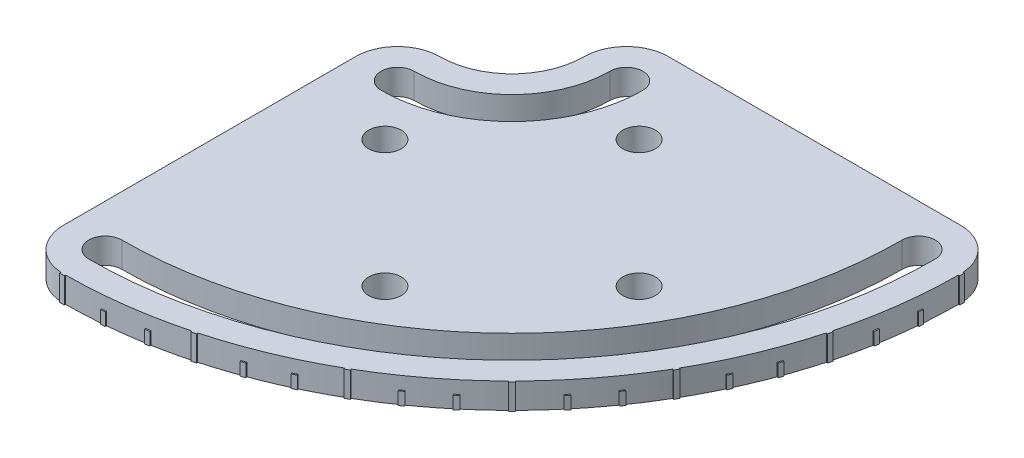
SolidWorks part; units mm, degrees
ref_plane "정면" through (0, 0, 0) normal (0, 0, 1) x (1, 0, 0)
ref_plane "윗면" through (0, 0, 0) normal (0, 1, 0) x (1, 0, 0)
ref_plane "우측면" through (0, 0, 0) normal (1, 0, 0) x (0, 0, -1)
sketch "스케치1" plane through (0, 0, 0) normal (0, 1, 0) x (1, 0, 0)
  line L1 (-8.25, -80) -> (-8.25, -22.5)
  line L7 (22.5, 8.25) -> (80, 8.25)
  arc A0 (0, -19.25) -> (0, -25.75) centre (0, -22.5) ccw
  arc A1 (25.75, 0) -> (19.25, 0) centre (22.5, 0) ccw
  arc A2 (0, -76.75) -> (0, -83.25) centre (0, -80) ccw
  arc A3 (83.25, 0) -> (76.75, 0) centre (80, 0) ccw
  arc A4 (0, -25.75) -> (25.75, 0) centre (0, 0) ccw
  arc A5 (0, -19.25) -> (19.25, 0) centre (0, 0) ccw
  arc A6 (0, -76.75) -> (76.75, 0) centre (0, 0) ccw
  arc A7 (0, -83.25) -> (83.25, 0) centre (0, 0) ccw
  circle A8 centre (58.75, -33.75) radius 3.2
  circle A9 centre (33.75, -58.75) radius 3.2
  circle A10 centre (8.75, -33.75) radius 3.2
  circle A11 centre (33.75, -8.75) radius 3.2
  arc A12 (0, -88.25) -> (88.25, 0) centre (0, 0) ccw
  arc A13 (0, -14.25) -> (14.25, 0) centre (0, 0) ccw
  arc A15 (-8.25, -80) -> (0, -88.25) centre (0, -80) ccw
  arc A16 (88.25, 0) -> (80, 8.25) centre (80, 0) ccw
  arc A17 (0, -14.25) -> (-8.25, -22.5) centre (0, -22.5) ccw
  arc A18 (22.5, 8.25) -> (14.25, 0) centre (22.5, 0) ccw
  point P0 (33.75, -33.75)
  point P26 (8.75, -33.75)
  point P27 (0, 0)
  dimension "D7" = 25
  dimension "D10" = 6.4
  dimension "D3" = 6.5
  dimension "D6" = 25
  dimension "D14" = 5
  dimension "D1" = 33.75
  dimension "D2" = 33.75
  dimension "D4" = 22.5
  dimension "D5" = 80
  dimension "D8" = 25
  dimension "D9" = 25
extrude "보스-돌출1" add sketch "스케치1" along normal blind 5
sketch "스케치2" plane through (0, 5, 0) normal (0, 1, 0) x (1, 0, 0)
  line L0 (0, 0) -> (-0.4634, -88.4988) construction
  line L1 (0, 0) -> (0.4634, -88.4988) construction
  line L2 (0, 0) -> (0, -88.5) construction
  line L3 (0.4581, -87.4988) -> (0.4634, -88.4988)
  line L4 (-0.4581, -87.4988) -> (-0.4634, -88.4988)
  arc A0 (-0.4634, -88.4988) -> (0.4634, -88.4988) centre (0, 0) ccw
  arc A1 (-0.4581, -87.4988) -> (0.4581, -87.4988) centre (0, 0) ccw
  dimension "D3" = 175
  dimension "D4" = 88.5
  dimension "D1" = 0.3
  dimension "D2" = 0.3
extrude "보스-돌출2" add sketch "스케치2" against normal up to surface (5 mm away) up to face at (12.7675, 0, 12.7675)
pattern_circular "원형 패턴1" count 7 over 90 about axis through (0, 0, 0) along (0, 1, 0) of "보스-돌출2"
sketch "스케치6" plane through (0, 0, 0) normal (0, -1, 0) x (1, 0, 0)
  line L2 (0, 0) -> (88.25, 0) construction
  line L3 (0, 0) -> (88.2488, 0.4621) construction
  line L6 (0, 0) -> (88.2371, -0.462) construction
  line L7 (88.4988, 0.4634) -> (87.9988, 0.4608)
  line L8 (88.4988, -0.4634) -> (87.9988, -0.4608)
  arc A1 (87.9988, -0.4608) -> (87.9988, 0.4608) centre (0, 0) ccw
  arc A2 (88.4988, -0.4634) -> (88.4988, 0.4634) centre (0, 0) ccw
  arc A4 (88.2488, 0.4621) -> (85.3614, 22.3941) centre (0, 0) ccw construction
  arc A5 (80, -8.25) -> (88.2371, -0.462) centre (80, 0) ccw construction
  dimension "D1" = 176
  dimension "D2" = 0.3
  dimension "D4" = 88.5
  dimension "D3" = 0.3
extrude "보스-돌출3" add sketch "스케치6" against normal blind 2.5
pattern_circular "원형 패턴2" count 19 over 90 about axis through (0, 5, 0) along (0, -1, 0) of "보스-돌출3"
